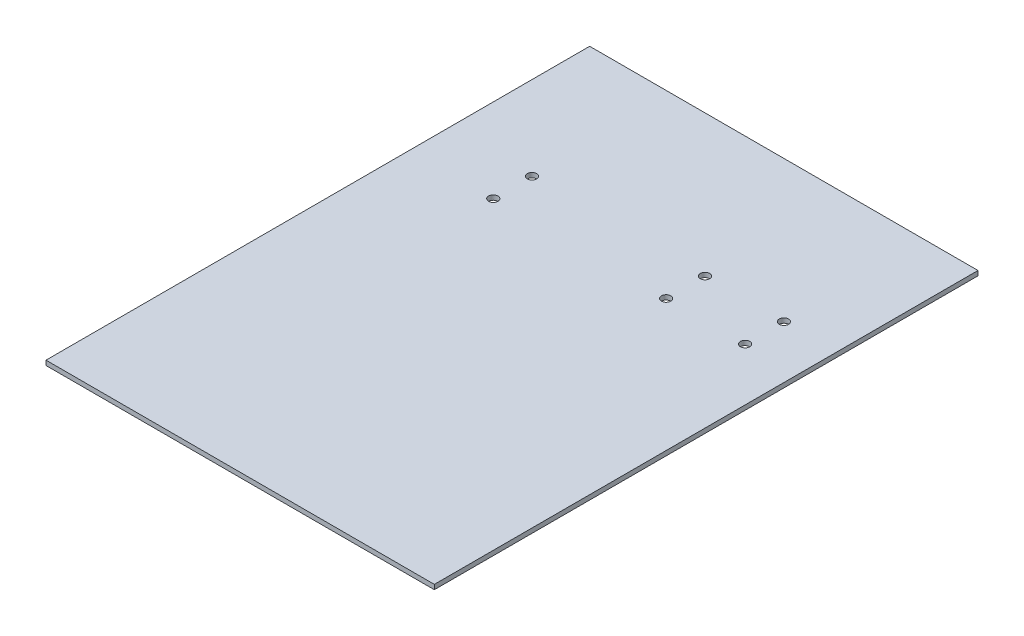
SolidWorks part; units mm, degrees
ref_plane "Front Plane" through (0, 0, 0) normal (0, 0, 1) x (1, 0, 0)
ref_plane "Top Plane" through (0, 0, 0) normal (0, 1, 0) x (1, 0, 0)
ref_plane "Right Plane" through (0, 0, 0) normal (1, 0, 0) x (0, 0, -1)
sketch "Sketch2" plane through (0, 0, 0) normal (0, 1, 0) x (1, 0, 0)
  line L1 (0, 0) -> (250, 0)
  line L2 (0, 0) -> (0, 350)
  line L3 (0, 350) -> (250, 350)
  line L4 (250, 0) -> (250, 350)
  dimension "D1" = 350
  dimension "D2" = 250
extrude "Boss-Extrude1" add sketch "Sketch2" along normal blind 3
hole_wizard "Ø6.0mm Dowel Hole3" positions "Sketch17" profile "Sketch18" hole size "Ø6.0" standard "ANSI Metric" end condition up to next
sketch "Sketch17" plane through (0, 0, 0) normal (0, -1, 0) x (-1, 0, 0)
  point P0 (-165.2429, 259)
  point P3 (-216.073, 259)
  point P6 (-216.073, 234)
  point P9 (-165.2429, 234)
sketch "Sketch18" plane through (165.2429, 0, -259) normal (1, 0, 0) x (0, 0, -1)
  line L0 (0, 0) -> (0, 3)
  line L1 (0, 3) -> (3, 3)
  line L2 (3, 3) -> (3, 0)
  line L5 (3, 0) -> (0, 0)
  line L11 (0, -6.35) -> (0, 107.95) construction
  dimension "Thru Hole Dia." = 6
  dimension "Thru Hole Depth" = 3
hole_wizard "Ø6.0mm Dowel Hole4" positions "Sketch19" profile "Sketch20" hole size "Ø6.0" standard "ANSI Metric" end condition up to next
sketch "Sketch19" plane through (0, 3, 0) normal (0, 1, 0) x (1, 0, 0)
  point P0 (53.9332, 259)
  point P3 (53.9332, 234)
  point P6 (0, 0)
  point P7 (0, 0)
sketch "Sketch20" plane through (53.9332, 3, -259) normal (1, 0, 0) x (0, 0, 1)
  line L0 (0, 0) -> (0, 3)
  line L1 (0, 3) -> (3, 3)
  line L2 (3, 3) -> (3, 0)
  line L5 (3, 0) -> (0, 0)
  line L11 (0, -6.35) -> (0, 107.95) construction
  dimension "Thru Hole Dia." = 6
  dimension "Thru Hole Depth" = 3
